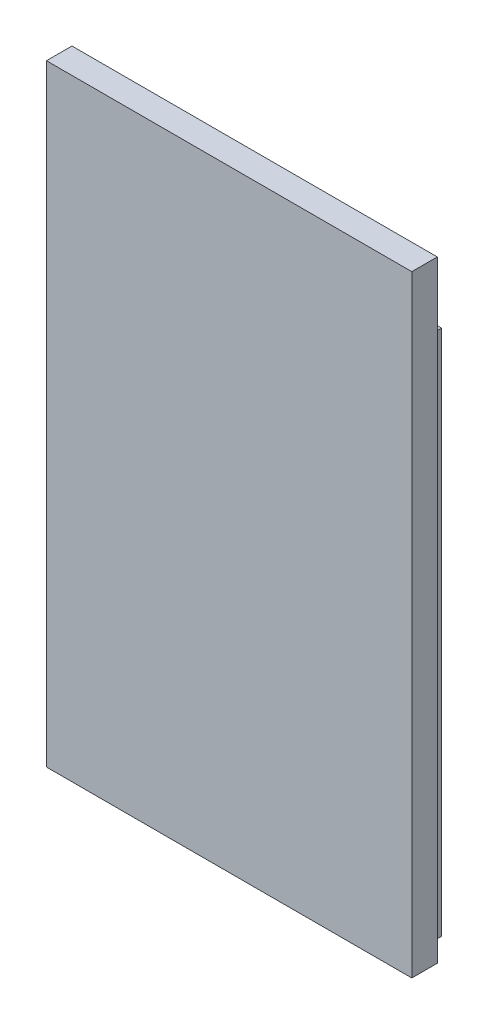
SolidWorks part; units mm, degrees
ref_plane "Front Plane" through (0, 0, 0) normal (0, 0, 1) x (1, 0, 0)
ref_plane "Top Plane" through (0, 0, 0) normal (0, 1, 0) x (1, 0, 0)
ref_plane "Right Plane" through (0, 0, 0) normal (1, 0, 0) x (0, 0, -1)
sketch "Sketch1" plane through (0, 0, 0) normal (0, 0, 1) x (1, 0, 0)
  line L1 (0, 0) -> (21.5, 0)
  line L2 (0, 0) -> (0, 36)
  line L3 (0, 36) -> (21.5, 36)
  line L4 (21.5, 0) -> (21.5, 36)
  dimension "D1" = 21.5
  dimension "D2" = 36
extrude "Boss-Extrude1" add sketch "Sketch1" along normal blind 1.5
sketch "Sketch2" plane through (0, 0, 1.5) normal (0, 0, 1) x (1, 0, 0)
  line L0 (0, 0) -> (21.5, 0) construction
  line L1 (20.25, 0) -> (19.25, 0)
  line L2 (20.25, 0) -> (20.25, 31)
  line L3 (20.25, 31) -> (19.25, 31)
  line L4 (19.25, 0) -> (19.25, 31)
  line L5 (21.5, 0) -> (21.5, 36) construction
  line L7 (19.25, 31) -> (3.75, 31)
  line L8 (19.25, 31) -> (19.25, 30)
  line L9 (19.25, 30) -> (3.75, 30)
  line L10 (3.75, 31) -> (3.75, 30)
  line L11 (4.75, 0) -> (19.25, 0)
  line L12 (3.75, 30) -> (4.75, 30)
  line L13 (3.75, 30) -> (3.75, 0)
  line L14 (3.75, 0) -> (4.75, 0)
  line L15 (4.75, 30) -> (4.75, 0)
  line L16 (4.75, 0) -> (4.75, 1)
  line L17 (4.75, 1) -> (19.25, 1)
  line L18 (19.25, 0) -> (19.25, 1)
  line M18 (0, 0) -> (21.5, 0)
  dimension "D2" = 1.25
  dimension "D3" = 1
  dimension "D4" = 31
  dimension "D5" = 15.5
  dimension "D6" = 1
  dimension "D7" = 1
  dimension "D8" = 1
extrude "Boss-Extrude2" add sketch "Sketch2" against normal blind 3 contours L15 L9 L13 M18 | L17 L15 L4 M18 | L4 L2 L3 M18 | L7 L10 L9 L4
